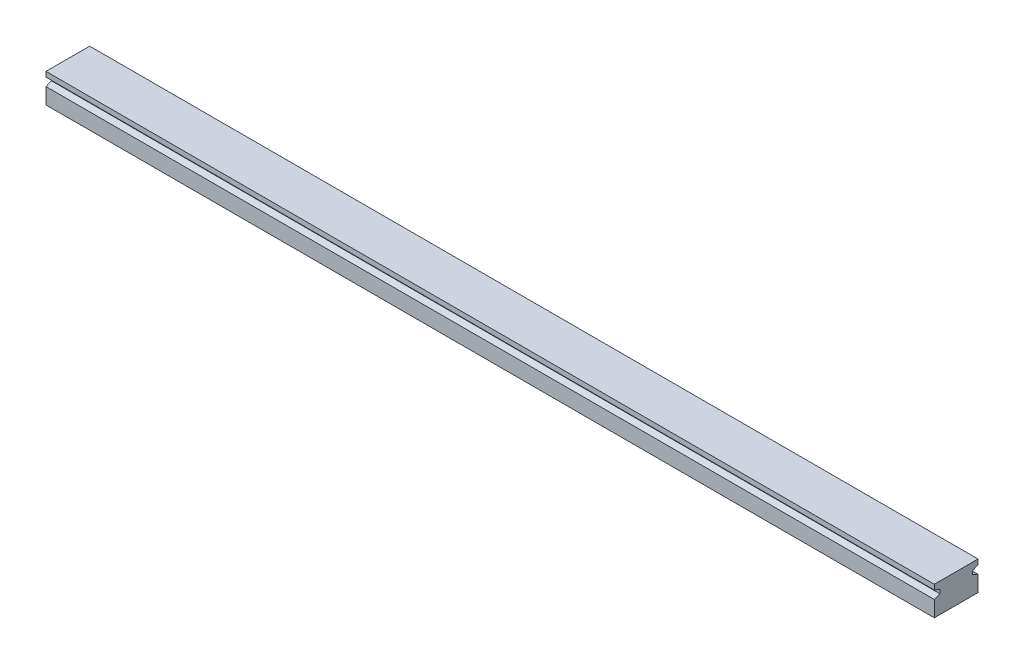
SolidWorks part; units mm, degrees
material "201 Annealed Stainless Steel (SS)"
ref_plane "Front Plane" through (0, 0, 0) normal (0, 0, 1) x (1, 0, 0)
ref_plane "Top Plane" through (0, 0, 0) normal (0, 1, 0) x (1, 0, 0)
ref_plane "Right Plane" through (0, 0, 0) normal (1, 0, 0) x (0, 0, -1)
sketch "Sketch2" plane through (0, 0, 0) normal (0, 1, 0) x (1, 0, 0)
  line L0 (-125, 0) -> (-75, 0) construction
  line L1 (-140, -6) -> (140, -6)
  line L2 (-140, -6) -> (-140, 6)
  line L3 (-140, 6) -> (140, 6)
  line L4 (140, -6) -> (140, 6)
  line L5 (-140, -6) -> (140, 6) construction
  line L6 (-140, 6) -> (140, -6) construction
  line L7 (-75, 0) -> (-25, 0) construction
  line L8 (-25, 0) -> (25, 0) construction
  line L9 (25, 0) -> (75, 0) construction
  line L10 (75, 0) -> (125, 0) construction
  circle A0 centre (-125, 0) radius 2
  circle A1 centre (-75, 0) radius 2
  circle A2 centre (-25, 0) radius 2
  circle A3 centre (25, 0) radius 2
  circle A4 centre (75, 0) radius 2
  circle A5 centre (125, 0) radius 2
  point P0 (0, 0)
  point P18 (0, 0)
  dimension "D4" = 4
  dimension "D1" = 280
  dimension "D2" = 12
  dimension "D3" = 50
extrude "Boss-Extrude1" add sketch "Sketch2" along normal mid plane 8
sketch "Sketch3" plane through (-140, 0, 0) normal (-1, 0, 0) x (0, 0, 1)
  line L5 (-6, 4) -> (-6, -4) construction
  line L7 (-6, 2.625) -> (-6, 0.375)
  line L9 (-4.5, 2) -> (-4.5, 1)
  line L10 (-6, -4) -> (6, -4) construction
  line L11 (-6, 4) -> (6, 4) construction
  line L12 (-4.5, 2) -> (-6, 2.625)
  line L13 (-6, 0.375) -> (-4.5, 1)
  line L14 (6, 2.625) -> (6, 0.375)
  line L15 (6, 4) -> (6, -4) construction
  line L16 (6, 0.375) -> (4.5, 1)
  line L17 (4.5, 1) -> (4.5, 2)
  line L18 (4.5, 2) -> (6, 2.625)
  dimension "D1" = 1.5
  dimension "D2" = 2.25
  dimension "D3" = 1
  dimension "D4" = 2
  dimension "D5" = 5
extrude "Cut-Extrude1" cut sketch "Sketch3" against normal through all
sketch "Sketch5" plane through (0, 4, 0) normal (0, 1, 0) x (1, 0, 0)
  circle A0 centre (-75, 0) radius 2
  circle A1 centre (-25, 0) radius 2
  circle A2 centre (25, 0) radius 2
  circle A3 centre (75, 0) radius 2
  circle A4 centre (75, 0) radius 2 construction
  circle A5 centre (25, 0) radius 2 construction
  circle A6 centre (-25, 0) radius 2 construction
  circle A7 centre (-75, 0) radius 2 construction
  circle A8 centre (-125, 0) radius 2
  circle A9 centre (125, 0) radius 2
  circle A10 centre (125, 0) radius 2 construction
  circle A11 centre (-125, 0) radius 2 construction
extrude "Boss-Extrude2" add sketch "Sketch5" against normal blind 2
sketch "Sketch4" plane through (0, 4, 0) normal (0, 1, 0) x (1, 0, 0)
  line L0 (-140, -6) -> (140, -6) construction
  line L1 (-140, 6) -> (-122, 6)
  line L2 (-140, 6) -> (-140, -6)
  line L3 (-140, -6) -> (-122, -6)
  line L4 (-122, 6) -> (-122, -6)
  dimension "D1" = 18
extrude "Cut-Extrude2" cut sketch "Sketch4" against normal through all
mirror "Mirror1" about plane through (0, 0, 0) normal (1, 0, 0) of "Cut-Extrude2"
sketch "Sketch7" plane through (0, -4, 0) normal (0, -1, 0) x (1, 0, 0)
  circle A0 centre (-75, 0) radius 2
  circle A1 centre (75, 0) radius 2
  circle A2 centre (75, 0) radius 2 construction
  circle A3 centre (-75, 0) radius 2 construction
extrude "Boss-Extrude3" add sketch "Sketch7" against normal through all
sketch "Sketch8" plane through (0, 2, 0) normal (0, -1, 0) x (1, 0, 0)
  circle A0 centre (-25, 0) radius 2
  circle A1 centre (-25, 0) radius 1.5
  circle A3 centre (25, 0) radius 2
  circle A4 centre (25, 0) radius 1.5
  circle A5 centre (25, 0) radius 2 construction
  circle A6 centre (-25, 0) radius 2 construction
  dimension "D1" = 3
extrude "Boss-Extrude4" add sketch "Sketch8" along normal blind 2
